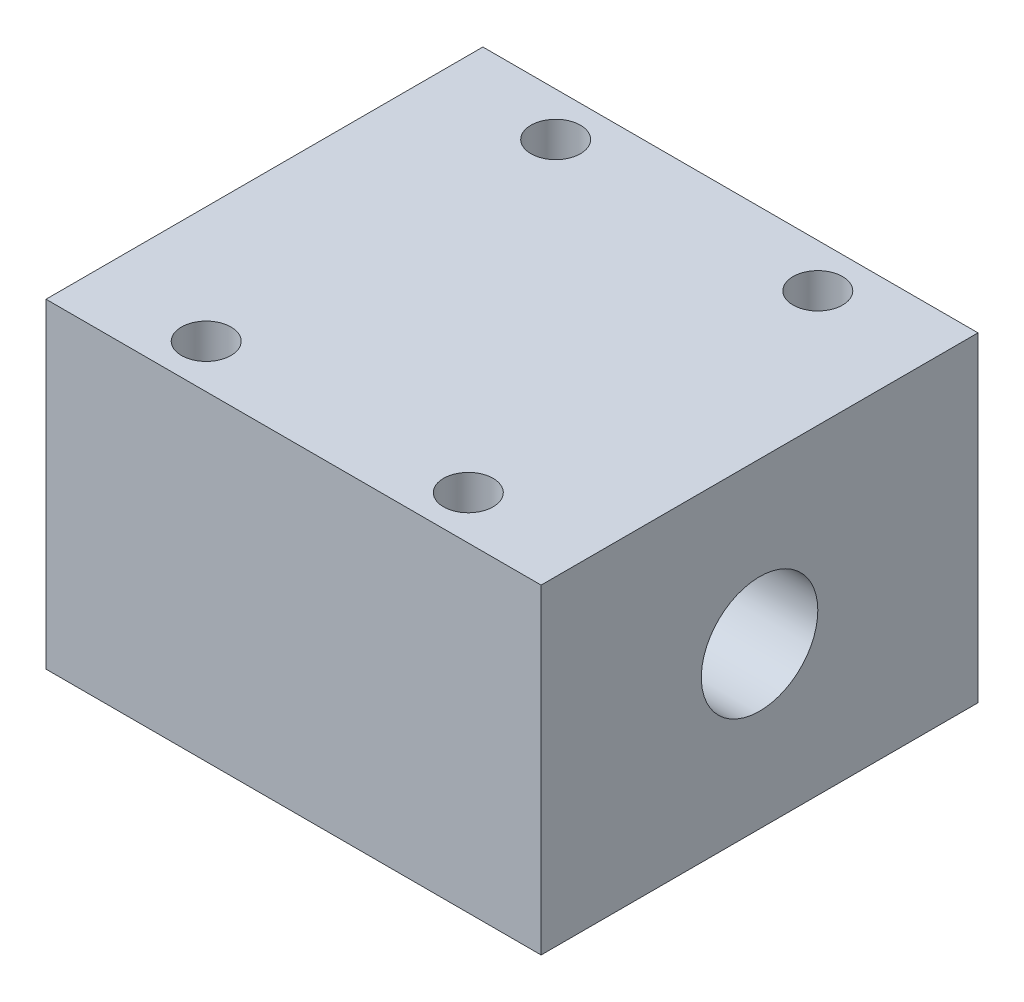
SolidWorks part; units mm, degrees
ref_plane "Front Plane" through (0, 0, 0) normal (0, 0, 1) x (1, 0, 0)
ref_plane "Top Plane" through (0, 0, 0) normal (0, 1, 0) x (1, 0, 0)
ref_plane "Right Plane" through (0, 0, 0) normal (1, 0, 0) x (0, 0, -1)
sketch "Sketch1" plane through (0, 0, 0) normal (0, 1, 0) x (1, 0, 0)
  line L0 (0, 15) -> (0, -15) construction
  line L1 (-17, 15) -> (17, 15)
  line L2 (-17, 15) -> (-17, -15)
  line L3 (-17, -15) -> (17, -15)
  line L4 (17, 15) -> (17, -15)
  line L5 (-17, 15) -> (17, -15) construction
  line L6 (-17, -15) -> (17, 15) construction
  line L7 (17, 0) -> (-17, 0) construction
  circle A0 centre (-9, 12) radius 1.7
  circle A1 centre (9, 12) radius 1.7
  circle A2 centre (9, -12) radius 1.7
  circle A3 centre (-9, -12) radius 1.7
  point P0 (0, 0)
  dimension "D4" = 3.4
  dimension "D5" = 3.4
  dimension "D1" = 30
  dimension "D2" = 34
  dimension "D3" = 9
  dimension "D6" = 24
  dimension "D7" = 24
  dimension "D8" = 9
extrude "Boss-Extrude1" add sketch "Sketch1" along normal blind 22
sketch "Sketch4" plane through (17, 0, 0) normal (1, 0, 0) x (0, 0, -1)
  line L0 (0, 22) -> (0, 0) construction
  line L1 (-15, 22) -> (15, 22) construction
  circle A0 centre (0, 11) radius 4
extrude "Cut-Extrude2" cut sketch "Sketch4" against normal blind 42
